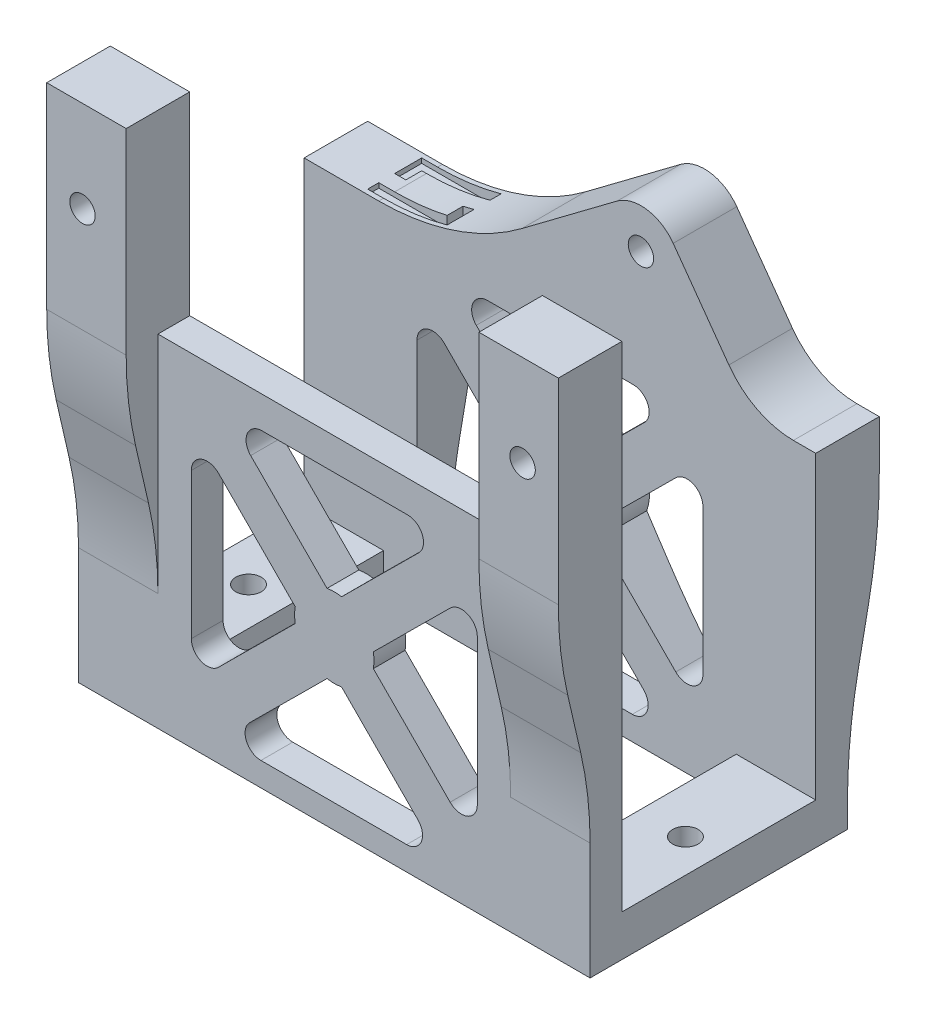
SolidWorks part; units mm, degrees
ref_plane "Alzado" through (0, 0, 0) normal (0, 0, 1) x (1, 0, 0)
ref_plane "Planta" through (0, 0, 0) normal (0, 1, 0) x (1, 0, 0)
ref_plane "Vista lateral" through (0, 0, 0) normal (1, 0, 0) x (0, 0, -1)
sketch "Croquis1" plane through (0, 0, 0) normal (0, 1, 0) x (1, 0, 0)
  line L0 (0, -55) -> (0, 55) construction
  line L1 (-16.1, -8.1) -> (-11.1, -8.1)
  line L2 (-16.1, -8.1) -> (-16.1, 8.1)
  line L3 (-16.1, 8.1) -> (-11.1, 8.1)
  line L4 (-11.1, -8.1) -> (-11.1, 8.1)
  line L5 (-16.1, -8.1) -> (-11.1, 8.1) construction
  line L6 (-16.1, 8.1) -> (-11.1, -8.1) construction
  line L7 (16.1, 8.1) -> (11.1, 8.1)
  line L8 (11.1, -8.1) -> (11.1, 8.1)
  line L9 (16.1, -8.1) -> (11.1, -8.1)
  line L10 (16.1, -8.1) -> (16.1, 8.1)
  point P0 (-13.6, 0)
  dimension "D1" = 5
  dimension "D2" = 16.2
  dimension "D3" = 16.1
extrude "Saliente-Extruir1" add sketch "Croquis1" along normal blind 3
sketch "Croquis2" plane through (0, 3, 0) normal (0, 1, 0) x (1, 0, 0)
  circle A0 centre (-13.5, 0) radius 0.8
  circle A1 centre (14, 0) radius 0.8
  dimension "D2" = 1.6
  dimension "D1" = 13.5
  dimension "D3" = 14
extrude "Cortar-Extruir2" cut sketch "Croquis2" against normal up to next (3 mm away)
sketch "Croquis4" plane through (0, 3, 0) normal (0, 1, 0) x (1, 0, 0)
  line L0 (16.1, -8.1) -> (16.1, 8.1) construction
  line L1 (-16.1, 8.1) -> (16.1, 8.1)
  line L2 (-16.1, 8.1) -> (-16.1, 6.1)
  line L3 (-16.1, 6.1) -> (16.1, 6.1)
  line L4 (16.1, 8.1) -> (16.1, 6.1)
  line L5 (-16.1, 8.1) -> (-16.1, -8.1) construction
  line L6 (16.1, -8.1) -> (-16.1, -8.1)
  line L7 (16.1, -8.1) -> (16.1, -6.1)
  line L8 (16.1, -6.1) -> (-16.1, -6.1)
  line L9 (-16.1, -8.1) -> (-16.1, -6.1)
  dimension "D1" = 2
extrude "Saliente-Extruir2" add sketch "Croquis4" along normal blind 18.5 and the other way blind 3
sketch "Croquis5" plane through (0, 0, 8.1) normal (0, 0, 1) x (1, 0, 0)
  line L0 (-16.1, 21.5) -> (16.1, 21.5) construction
  line L1 (16.1, 21.5) -> (11.1, 21.5)
  line L2 (16.1, 21.5) -> (16.1, 33.7)
  line L3 (16.1, 33.7) -> (11.1, 33.7)
  line L4 (11.1, 21.5) -> (11.1, 33.7)
  line L6 (-16.1, 21.5) -> (-11.1, 21.5)
  line L7 (-16.1, 21.5) -> (-16.1, 33.7)
  line L8 (-16.1, 33.7) -> (-11.1, 33.7)
  line L9 (-11.1, 21.5) -> (-11.1, 33.7)
  dimension "D1" = 5
  dimension "D2" = 12.2
  dimension "D3" = 5
extrude "Saliente-Extruir3" add sketch "Croquis5" against normal blind 2
sketch "Croquis7" plane through (-16.1, 0, 0) normal (-1, 0, 0) x (0, 0, 1)
  line L1 (8.1, 7.353) -> (8.1, 0) construction
  line L4 (10.1, 33.7) -> (8.1, 33.7)
  line L7 (10.1, 21.347) -> (10.1, 33.7)
  line L9 (8.693, 12.5797) -> (9.507, 16.1203)
  line L10 (6.1, 33.7) -> (8.1, 33.7) construction
  line L11 (8.1, 7.353) -> (8.1, 33.7)
  arc A0 (9.507, 16.1203) -> (10.1, 21.347) centre (-13.2292, 21.347) ccw
  arc A1 (8.693, 12.5797) -> (8.1, 7.353) centre (31.4292, 7.353) ccw
  point P13 (10.1, 18.7)
  point P16 (8.1, 10)
  dimension "D3" = 23.3292
  dimension "D1" = 2
  dimension "D2" = 15
  dimension "D5" = 10
extrude "Saliente-Extruir4" add sketch "Croquis7" against normal through all
sketch "Croquis8" plane through (0, 33.7, 0) normal (0, 1, 0) x (1, 0, 0)
  line L0 (-11.1, -10.1) -> (-11.1, -8.1)
  line L1 (16.1, -10.1) -> (-16.1, -10.1) construction
  line L2 (-11.1, -8.1) -> (11.1, -8.1)
  line L3 (11.1, -8.1) -> (11.1, -10.1)
  line L4 (11.1, -10.1) -> (-11.1, -10.1)
extrude "Cortar-Extruir3" cut sketch "Croquis8" against normal up to next and the other way through all
sketch "Croquis9" plane through (0, 0, 10.1) normal (0, 0, 1) x (1, 0, 0)
  line L0 (-11.1, 21.347) -> (-11.1, 33.7) construction
  line L2 (-11.1, 33.7) -> (-16.1, 33.7) construction
  line L3 (0, -11.11) -> (0, 11.11) construction
  circle A1 centre (-13.85, 27.95) radius 0.8
  circle A2 centre (13.85, 27.95) radius 0.8
  dimension "D2" = 1.6
  dimension "D3" = 2.75
  dimension "D4" = 5.75
extrude "Cortar-Extruir4" cut sketch "Croquis9" against normal up to next
sketch "Croquis10" plane through (0, 0, -8.1) normal (0, 0, -1) x (-1, 0, 0)
  line L1 (-16.1, 21.5) -> (-14.6945, 21.5) construction
  line L2 (-16.1, 21.5) -> (16.1, 21.5) construction
  line L3 (-10.634, 23.5824) -> (-7.1303, 28.4588)
  line L4 (-3.6, 29) -> (2.4, 24.5)
  line L5 (11.4, 21.5) -> (16.1, 21.5) construction
  line L6 (-14.6945, 21.5) -> (11.4, 21.5)
  line L7 (-11.1, 33.7) -> (-11.1, 21.5) construction
  circle A0 centre (-5.1, 27) radius 0.8
  arc A1 (-3.6, 29) -> (-7.1303, 28.4588) centre (-5.1, 27) ccw
  arc A2 (-14.6945, 21.5) -> (-10.634, 23.5824) centre (-14.6945, 26.5) ccw
  arc A3 (2.4, 24.5) -> (11.4, 21.5) centre (11.4, 36.5) ccw
  point P14 (-12.1303, 21.5)
  point P21 (6.4, 21.5)
  dimension "D1" = 1.6
  dimension "D4" = 5
  dimension "D7" = 5
  dimension "D8" = 15
  dimension "D2" = 6
  dimension "D3" = 27
  dimension "D5" = 10
  dimension "D6" = 5
extrude "Saliente-Extruir5" add sketch "Croquis10" along normal mid plane 4
sketch "Croquis13" plane through (-16.1, 0, 0) normal (-1, 0, 0) x (0, 0, 1)
  line L0 (-8.1, 21.5) -> (-10.1, 21.5)
  line L1 (-10.1, 21.5) -> (-10.1, 18.4657)
  line L2 (-9.4203, 11.6016) -> (-8.7797, 8.3984)
  line L3 (-8.1, 21.5) -> (-8.1, 0) construction
  line L4 (-8.1, 1.5343) -> (-8.1, 0) construction
  line L5 (-8.1, 1.5343) -> (-8.1, 21.5)
  arc A0 (-8.7797, 8.3984) -> (-8.1, 1.5343) centre (-43.1, 1.5343) cw
  arc A1 (-10.1, 18.4657) -> (-9.4203, 11.6016) centre (24.9, 18.4657) ccw
  point P12 (-8.1, 5)
  point P15 (-10.1, 15)
  dimension "D3" = 35
  dimension "D1" = 5
  dimension "D2" = 10
extrude "Saliente-Extruir7" add sketch "Croquis13" against normal through all
sketch "Croquis14" plane through (0, 0, 8.1) normal (0, 0, 1) x (1, 0, 0)
  line L0 (-9, 15.1169) -> (-9, 5.9455)
  line L1 (-7.2952, 5.2361) -> (-2.4577, 10.0423)
  line L2 (-2.4578, 10.9575) -> (-7.2906, 15.8218)
  line L3 (-16.1, 0) -> (16.1, 0) construction
  line L4 (0, 0) -> (0, 27.7062) construction
  line L5 (-5.2639, 17.7952) -> (-0.4577, 12.9577)
  line L6 (0.4575, 12.9578) -> (5.3218, 17.7906)
  line L7 (4.6169, 19.5) -> (-4.5545, 19.5)
  line L8 (7.2952, 15.7639) -> (2.4577, 10.9577)
  line L9 (2.4578, 10.0425) -> (7.2906, 5.1782)
  line L10 (9, 5.8831) -> (9, 15.0545)
  line L11 (5.2639, 3.2048) -> (0.4577, 8.0423)
  line L12 (-0.4575, 8.0422) -> (-5.3218, 3.2094)
  line L13 (-4.6169, 1.5) -> (4.5545, 1.5)
  circle A1 centre (0, 10.5) radius 2.5 construction
  arc A2 (-9, 5.9455) -> (-7.2952, 5.2361) centre (-8, 5.9455) ccw
  arc A3 (-9, 15.1169) -> (-7.2906, 15.8218) centre (-8, 15.1169) cw
  arc A4 (-2.4577, 10.0423) -> (-2.4578, 10.9575) centre (0, 10.5) cw
  arc A5 (-0.4577, 12.9577) -> (0.4575, 12.9578) centre (0, 10.5) cw
  arc A6 (4.6169, 19.5) -> (5.3218, 17.7906) centre (4.6169, 18.5) cw
  arc A7 (-4.5545, 19.5) -> (-5.2639, 17.7952) centre (-4.5545, 18.5) ccw
  arc A8 (2.4577, 10.9577) -> (2.4578, 10.0425) centre (0, 10.5) cw
  arc A9 (9, 5.8831) -> (7.2906, 5.1782) centre (8, 5.8831) cw
  arc A10 (9, 15.0545) -> (7.2952, 15.7639) centre (8, 15.0545) ccw
  arc A11 (0.4577, 8.0423) -> (-0.4575, 8.0422) centre (0, 10.5) cw
  arc A12 (-4.6169, 1.5) -> (-5.3218, 3.2094) centre (-4.6169, 2.5) cw
  arc A13 (4.5545, 1.5) -> (5.2639, 3.2048) centre (4.5545, 2.5) ccw
  point P15 (-9, 3.5423)
  point P18 (-9, 17.5423)
  point P47 (0, 10.5)
  dimension "D4" = 5
  dimension "D7" = 1
  dimension "D1" = 14
  dimension "D2" = 9
  dimension "D3" = 6.5
  dimension "D5" = 10.5
  dimension "D6" = 2.4577
  dimension "D8" = 4
extrude "Cortar-Extruir5" cut sketch "Croquis14" against normal through all
sketch "Croquis20" plane through (0, 21.5, 0) normal (0, 1, 0) x (1, 0, 0)
  line L0 (-12.4, 6.4) -> (-7.4, 6.4)
  line L1 (-7.4, 6.4) -> (-7.4, 8.1)
  line L2 (-7.4, 8.1) -> (-8.1, 8.1)
  line L3 (-8.1, 8.1) -> (-8.1, 7.1)
  line L4 (-8.1, 7.1) -> (-12.4, 7.1)
  line L5 (-12.4, 7.1) -> (-12.4, 6.4)
  line L6 (-6.9, 8.1) -> (-12.9, 8.1) construction
  line L7 (-11.4, 6.1) -> (-2.4, 6.1) construction
  line L8 (-9.9, 10.8512) -> (-9.9, 4.8203) construction
  line L9 (-2.4, 10.1) -> (-2.4, 6.1) construction
  line L10 (-7.4, 9.1) -> (-7.4, 9.8)
  line L11 (-7.4, 9.8) -> (-12.4, 9.8)
  line L12 (-12.4, 9.8) -> (-12.4, 8.1)
  line L13 (-12.4, 8.1) -> (-11.7, 8.1)
  line L14 (-11.7, 8.1) -> (-11.7, 9.1)
  line L15 (-11.7, 9.1) -> (-7.4, 9.1)
  point P15 (-9.9, 8.1)
  point P16 (-9.9, 9.8)
  point P23 (-9.9, 8.1)
  dimension "D1" = 0.7
  dimension "D2" = 5
  dimension "D3" = 0.7
  dimension "D4" = 1
  dimension "D5" = 2
  dimension "D6" = 1.8
  dimension "D7" = 5
  dimension "D8" = 6
  dimension "D9" = 3
  dimension "D10" = 2
extrude "Cortar-Extruir9" cut sketch "Croquis20" against normal blind 0.3 and the other way up to next
sketch "Croquis21" plane through (0, 3, 0) normal (0, 1, 0) x (1, 0, 0)
  line L1 (-16.1, 6.1) -> (16.1, 6.1)
  line L2 (-16.1, 6.1) -> (-16.1, -6.1)
  line L3 (-16.1, -6.1) -> (16.1, -6.1)
  line L4 (16.1, 6.1) -> (16.1, -6.1)
extrude "Cortar-Extruir10" cut sketch "Croquis21" against normal blind 0.4
equation "\"0.0.5mm\"=0.2"
